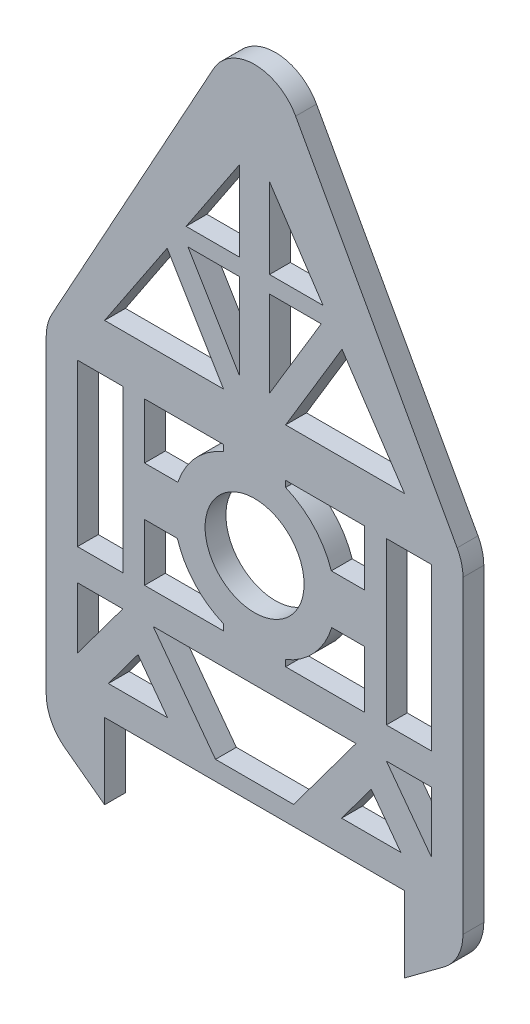
SolidWorks part; units mm, degrees
ref_plane "Front Plane" through (0, 0, 0) normal (0, 0, 1) x (1, 0, 0)
ref_plane "Top Plane" through (0, 0, 0) normal (0, 1, 0) x (1, 0, 0)
ref_plane "Right Plane" through (0, 0, 0) normal (1, 0, 0) x (0, 0, -1)
sketch "Sketch1" plane through (0, 0, 0) normal (0, 0, 1) x (1, 0, 0)
  line L0 (-194.4852, -273.0502) -> (93.4037, -273.0502)
  line L1 (149.4593, -273.0502) -> (149.4593, 26.9498)
  line L2 (-250.5407, 26.9498) -> (-250.5407, -273.0502)
  line L3 (-250.5407, -273.0502) -> (-250.5407, -304.0396)
  line L4 (149.4593, 26.9498) -> (155.0148, 21.3942)
  line L5 (-220.5407, -174.0943) -> (-177.0313, -174.0943)
  line L6 (-220.5407, -232.6652) -> (-177.0313, -174.0943)
  line L7 (-88.0382, -254.669) -> (-147.8931, -174.0943)
  line L8 (-13.0433, -254.669) -> (46.8116, -174.0943)
  line L9 (89.8021, -243.0502) -> (32.9594, -243.0502)
  line L10 (-220.5407, -144.0943) -> (-177.0313, -144.0943)
  line L11 (-64.8811, 251.3559) -> (-116.294, 174.2367)
  line L12 (93.4037, 56.9498) -> (33.3815, 146.9831)
  line L13 (-194.4852, 56.9498) -> (-80.3129, 56.9498)
  line L14 (119.4593, -232.6652) -> (75.9498, -174.0943)
  line L15 (-220.5407, 10.9057) -> (-177.0313, 10.9057)
  line L16 (-220.5407, 10.9057) -> (-220.5407, -51.5924)
  line L17 (119.4593, -144.0943) -> (119.4593, -94.2592)
  line L18 (-250.5407, -304.0396) -> (-194.4852, -345.6805)
  line L19 (-162.4622, -157.2967) -> (-162.4622, -181.3495) construction
  line L20 (32.9594, -243.0502) -> (61.3807, -204.7904)
  line L21 (-88.0382, -254.669) -> (-13.0433, -254.669)
  line L22 (89.8021, -243.0502) -> (61.3807, -204.7904)
  line L23 (-190.8835, -243.0502) -> (-134.0409, -243.0502)
  line L24 (-20.7685, 56.9498) -> (93.4037, 56.9498)
  line L25 (-190.8835, -243.0502) -> (-162.4622, -204.7904)
  line L26 (75.9498, -174.0943) -> (119.4593, -174.0943)
  line L27 (-147.8931, -174.0943) -> (46.8116, -174.0943)
  line L28 (-134.0409, -243.0502) -> (-162.4622, -204.7904)
  line L29 (-194.4852, -345.6805) -> (-194.4852, -273.0502)
  line L30 (93.4037, -345.6805) -> (93.4037, -273.0502)
  line L31 (-116.294, 174.2367) -> (-64.8811, 174.2367)
  line L32 (-50.5407, 151.8053) -> (-50.5407, 389.926) construction
  line L33 (-250.5407, 26.9498) -> (-50.5407, 389.926)
  line L34 (-50.5407, 151.8053) -> (-50.5407, 80.4357) construction
  line L35 (-50.5407, 389.926) -> (149.4593, 26.9498)
  line L36 (-177.0313, 10.9057) -> (-177.0313, -51.5924)
  line L37 (-156.1677, 10.9057) -> (-156.1677, -42.4396)
  line L38 (-177.0313, -144.0943) -> (-177.0313, -94.2592)
  line L39 (-156.1677, -144.0943) -> (-156.1677, -89.3282)
  line L40 (149.4593, -304.0396) -> (93.4037, -345.6805)
  line L41 (149.4593, -273.0502) -> (149.4593, -304.0396)
  line L42 (-250.5407, -273.0502) -> (-250.5407, -304.0396)
  line L43 (149.4593, -273.0502) -> (149.4593, -304.0396)
  line L44 (-220.5407, -174.0943) -> (-220.5407, -232.6652)
  line L45 (119.4593, -174.0943) -> (119.4593, -232.6652)
  line L46 (-80.3129, -138.1475) -> (-80.3129, -144.0943)
  line L47 (-20.7685, -138.1475) -> (-20.7685, -144.0943)
  line L48 (-80.3129, 4.9589) -> (-80.3129, 10.9057)
  line L49 (-20.7685, 4.9589) -> (-20.7685, 10.9057)
  line L50 (55.0862, -144.0943) -> (55.0862, -89.3282)
  line L51 (75.9498, -144.0943) -> (75.9498, -94.2592)
  line L52 (55.0862, 10.9057) -> (55.0862, -42.4396)
  line L53 (75.9498, 10.9057) -> (75.9498, -51.5924)
  line L54 (-220.5407, -94.2592) -> (-220.5407, -144.0943)
  line L55 (13.4432, 158.0323) -> (-36.2003, 158.0323)
  line L56 (15.2125, 174.2367) -> (-36.2003, 251.3559)
  line L57 (-64.8811, 251.3559) -> (-64.8811, 174.2367)
  line L58 (-36.2003, 251.3559) -> (-36.2003, 174.2367)
  line L59 (-114.5246, 158.0323) -> (-64.8811, 75.4918)
  line L60 (-134.463, 146.9831) -> (-80.3129, 56.9498)
  line L61 (13.4432, 158.0323) -> (-36.2003, 75.4918)
  line L62 (33.3815, 146.9831) -> (-20.7685, 56.9498)
  line L63 (-36.2003, 174.2367) -> (15.2125, 174.2367)
  line L64 (-64.8811, 158.0323) -> (-114.5246, 158.0323)
  line L65 (-64.8811, 158.0323) -> (-64.8811, 75.4918)
  line L66 (-36.2003, 158.0323) -> (-36.2003, 75.4918)
  line L67 (-134.463, 146.9831) -> (-194.4852, 56.9498)
  line L68 (119.4593, -51.5924) -> (119.4593, 10.9057)
  line L69 (55.0862, -89.3282) -> (23.5499, -89.3282)
  line L70 (55.0862, -42.4396) -> (23.0989, -42.4396)
  line L71 (-156.1677, -89.3282) -> (-124.6314, -89.3282)
  line L72 (-156.1677, -42.4396) -> (-124.1804, -42.4396)
  line L73 (-156.1677, 10.9057) -> (-80.3129, 10.9057)
  line L74 (-156.1677, -144.0943) -> (-80.3129, -144.0943)
  line L75 (75.9498, -144.0943) -> (119.4593, -144.0943)
  line L76 (75.9498, 10.9057) -> (119.4593, 10.9057)
  line L77 (-20.7685, 10.9057) -> (55.0862, 10.9057)
  line L78 (-20.7685, -144.0943) -> (55.0862, -144.0943)
  line L79 (119.4593, -51.5924) -> (119.4593, -94.2592)
  line L80 (75.9498, -51.5924) -> (75.9498, -94.2592)
  line L81 (-177.0313, -51.5924) -> (-177.0313, -94.2592)
  line L82 (-220.5407, -51.5924) -> (-220.5407, -94.2592)
  arc A0 (-124.6314, -89.3282) -> (-80.3129, -138.1475) centre (-50.5407, -66.5943) ccw
  circle A1 centre (-50.5407, -66.5943) radius 47.5
  arc A2 (23.0989, -42.4396) -> (-20.7685, 4.9589) centre (-50.5407, -66.5943) ccw
  arc A3 (-80.3129, 4.9589) -> (-124.1804, -42.4396) centre (-50.5407, -66.5943) ccw
  arc A4 (-20.7685, -138.1475) -> (23.5499, -89.3282) centre (-50.5407, -66.5943) ccw
  point P40 (-177.0313, -119.1768)
  point P53 (75.9498, -119.1768)
  point P90 (-198.786, -144.0943)
  dimension "D1" = 53.393
  dimension "D2" = 155
extrude "Boss-Extrude1" add sketch "Sketch1" along normal blind 20 contours L41 L1 L35 L33 L2 L3 L18 L29 L0 L30 L40 A1 L82 L16 L15 L36 L81 L38 L10 L54 L80 L53 L76 L68 L79 L17 L75 L51 L67 L60 L13 L66 L55 L61 L63 L58 L56 L62 L12 L24 L44 L5 L6
fillet "Fillet1" radius 45 5 edges at (-250.5407, -304.0396, 10) (149.4593, -304.0396, 10) (149.4593, 26.9498, 10) (-250.5407, 26.9498, 10) (-50.5407, 389.926, 10)
